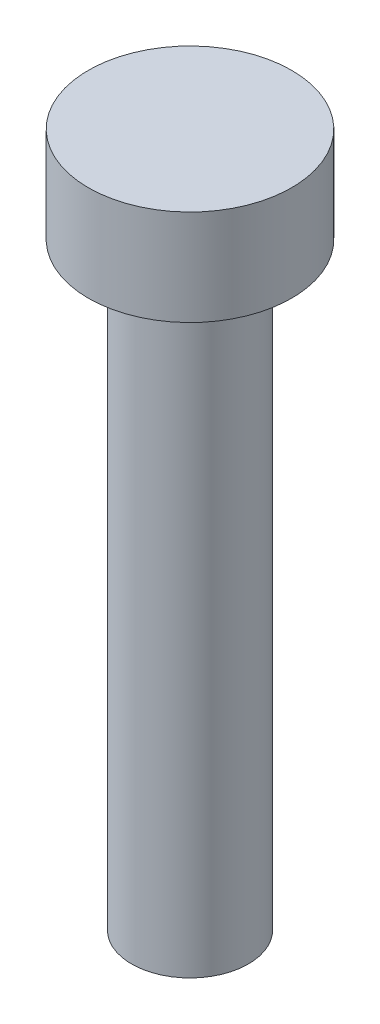
SolidWorks part; units mm, degrees
ref_plane "Front Plane" through (0, 0, 0) normal (0, 0, 1) x (1, 0, 0)
ref_plane "Top Plane" through (0, 0, 0) normal (0, 1, 0) x (1, 0, 0)
ref_plane "Right Plane" through (0, 0, 0) normal (1, 0, 0) x (0, 0, -1)
sketch "Sketch1" plane through (0, 0, 0) normal (0, 1, 0) x (1, 0, 0)
  circle A0 centre (0, 0) radius 4.25
  dimension "D1" = 8.5
extrude "Boss-Extrude1" add sketch "Sketch1" along normal blind 4
sketch "Sketch2" plane through (0, 0, 0) normal (0, -1, 0) x (1, 0, 0)
  circle A0 centre (0, 0) radius 2.44
  dimension "D1" = 4.88
extrude "Boss-Extrude2" add sketch "Sketch2" along normal blind 25
